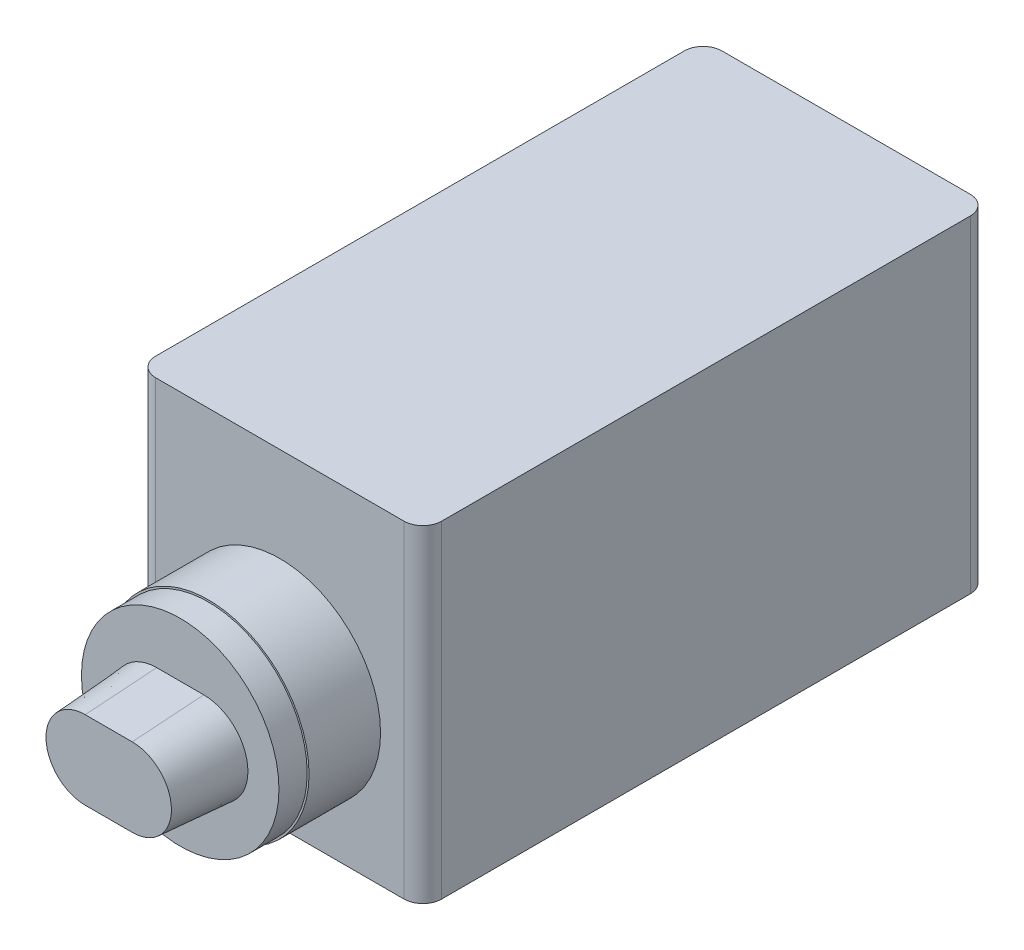
SolidWorks part; units mm, degrees
ref_plane "Front Plane" through (0, 0, 0) normal (0, 0, 1) x (1, 0, 0)
ref_plane "Top Plane" through (0, 0, 0) normal (0, 1, 0) x (1, 0, 0)
ref_plane "Right Plane" through (0, 0, 0) normal (1, 0, 0) x (0, 0, -1)
sketch "Sketch1" plane through (0, 0, 0) normal (0, 1, 0) x (1, 0, 0)
  line L0 (7.6, -15.05) -> (-7.6, -15.05)
  line L1 (7.6, -15.05) -> (7.6, 15.05)
  line L2 (7.6, 15.05) -> (-7.6, 15.05)
  line L3 (-7.6, -15.05) -> (-7.6, 15.05)
  line L4 (7.6, -15.05) -> (-7.6, 15.05) construction
  line L5 (7.6, 15.05) -> (-7.6, -15.05) construction
  point P0 (0, 0)
  dimension "D1" = 15.2
  dimension "D2" = 30.1
extrude "Boss-Extrude1" add sketch "Sketch1" along normal blind 17.4
fillet "Fillet1" radius 1 4 edges at (-7.6, 8.7, -15.05) (7.6, 8.7, -15.05) (-7.6, 8.7, 15.05) (7.6, 8.7, 15.05)
sketch "Sketch3" plane through (0, 0, 15.05) normal (0, 0, 1) x (1, 0, 0)
  circle A0 centre (0, 7.0307) radius 5.35
  dimension "D1" = 10.7
extrude "Boss-Extrude2" add sketch "Sketch3" along normal blind 3.8
sketch "Sketch4" plane through (0, 0, 18.85) normal (0, 0, 1) x (1, 0, 0)
  circle A0 centre (0, 7.0307) radius 5.25
  circle A2 centre (0, 7.0307) radius 5.35 construction
  dimension "D1" = 0.1
extrude "Boss-Extrude3" add sketch "Sketch4" along normal blind 1.5
sketch "Sketch5" plane through (0, 0, 20.35) normal (0, 0, 1) x (1, 0, 0)
  line L0 (-1.25, 7.0307) -> (1.25, 7.0307) construction
  line L1 (-1.25, 9.3807) -> (1.25, 9.3807)
  line L2 (-1.25, 4.6807) -> (1.25, 4.6807)
  arc A0 (-1.25, 9.3807) -> (-1.25, 4.6807) centre (-1.25, 7.0307) ccw
  arc A1 (1.25, 4.6807) -> (1.25, 9.3807) centre (1.25, 7.0307) ccw
  circle A2 centre (0, 7.0307) radius 5.25 construction
  point P3 (0, 7.0307)
  dimension "D1" = 2.5
  dimension "D2" = 4.7
extrude "Boss-Extrude4" add sketch "Sketch5" along normal blind 3.8 draft 4
